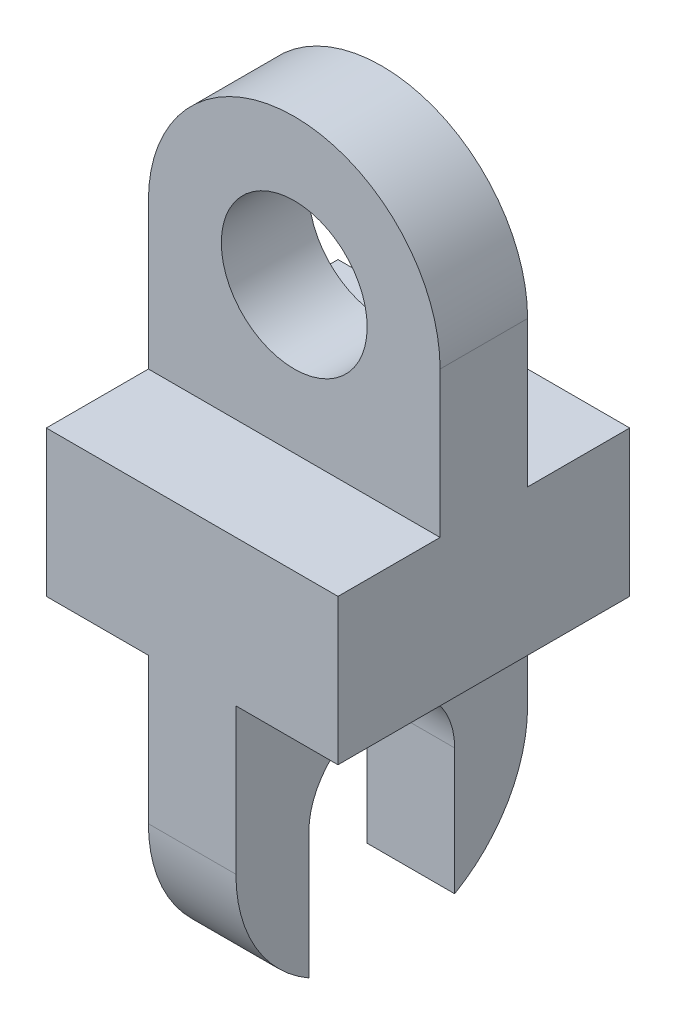
SolidWorks part; units mm, degrees
ref_plane "Alzado" through (0, 0, 0) normal (0, 0, 1) x (1, 0, 0)
ref_plane "Planta" through (0, 0, 0) normal (0, 1, 0) x (1, 0, 0)
ref_plane "Vista lateral" through (0, 0, 0) normal (1, 0, 0) x (0, 0, -1)
sketch "Croquis3" plane through (0, 0, 0) normal (0, 0, 1) x (1, 0, 0)
  line L2 (-50, 100) -> (-50, -100)
  line L3 (-50, -100) -> (50, -100)
  line L4 (50, 100) -> (50, -100)
  arc A0 (50, 100) -> (-50, 100) centre (0, 100) ccw
  point P0 (0, 0)
  dimension "D3" = 100
  dimension "D1" = 100
  dimension "D2" = 200
  dimension "D4" = 50
extrude "Saliente-Extruir1" add sketch "Croquis3" along normal blind 100
sketch "Croquis5" plane through (0, 0, 100) normal (0, 0, 1) x (1, 0, 0)
  line L0 (50, -100) -> (50, 100) construction
  line L2 (-50, 100) -> (-50, 0)
  line L3 (-50, 0) -> (50, 0)
  line L4 (50, 100) -> (50, 0)
  arc A0 (50, 100) -> (-50, 100) centre (0, 100) ccw
  arc A2 (50, 100) -> (-50, 100) centre (0, 100) ccw construction
  point P0 (0, 66.3558)
  dimension "D1" = 100
  dimension "D2" = 100
sketch "Croquis8" plane through (0, 0, 100) normal (0, 0, 1) x (1, 0, 0)
  line L0 (50, 100) -> (50, 0) construction
  line L2 (-50, 100) -> (-50, 50)
  line L3 (-50, 50) -> (50, 50)
  line L4 (50, 100) -> (50, 50)
  arc A0 (50, 100) -> (-50, 100) centre (0, 100) ccw
  arc A1 (50, 100) -> (-50, 100) centre (0, 100) ccw construction
  point P6 (0, 75)
  dimension "D1" = 100
  dimension "D2" = 50
extrude "Cortar-Extruir4" cut sketch "Croquis8" against normal blind 35 and the other way through all
sketch "Croquis9" plane through (0, 0, 0) normal (0, 0, -1) x (-1, 0, 0)
  line L0 (50, 100) -> (50, 0) construction
  line L2 (-50, 100) -> (-50, 50)
  line L3 (-50, 50) -> (50, 50)
  line L4 (50, 100) -> (50, 50)
  arc A0 (50, 100) -> (-50, 100) centre (0, 100) ccw
  arc A1 (50, 100) -> (-50, 100) centre (0, 100) ccw construction
  point P5 (0, 75)
  dimension "D1" = 100
  dimension "D2" = 50
extrude "Cortar-Extruir5" cut sketch "Croquis9" against normal blind 35
sketch "Croquis10" plane through (0, 0, 35) normal (0, 0, -1) x (-1, 0, 0)
  circle A0 centre (0, 100) radius 25
  arc A1 (50, 100) -> (-50, 100) centre (0, 100) ccw construction
  dimension "D1" = 50
extrude "Cortar-Extruir6" cut sketch "Croquis10" against normal through all both and the other way through all
sketch "Croquis12" plane through (-50, 0, 0) normal (-1, 0, 0) x (0, 0, 1)
  line L0 (100, 50) -> (100, -100) construction
  line L1 (0, 0) -> (100, 0)
  line L2 (0, 0) -> (0, -100)
  line L3 (0, -100) -> (100, -100)
  line L4 (100, 0) -> (100, -100)
  line L5 (0, 0) -> (100, -100) construction
  line L6 (0, -100) -> (100, 0) construction
  line L9 (100, -100) -> (0, -100) construction
  point P0 (50, -50)
  dimension "D1" = 100
  dimension "D2" = 0
  dimension "D3" = 100
extrude "Cortar-Extruir10" cut sketch "Croquis12" against normal through all and the other way through all
sketch "Croquis17" plane through (-50, 0, 0) normal (-1, 0, 0) x (0, 0, 1)
  line L0 (0, 50) -> (0, 0) construction
  line L1 (0, 0) -> (100, 0) construction
  line L4 (0, 0) -> (100, 0)
  line L5 (0, 0) -> (0, -50)
  line L7 (100, 0) -> (100, -50)
  arc A0 (0, -50) -> (100, -50) centre (50, -50) ccw
  dimension "D1" = 100
  dimension "D2" = 50
extrude "Saliente-Extruir3" add sketch "Croquis17" against normal blind 100
sketch "Croquis22" plane through (-50, 0, 0) normal (-1, 0, 0) x (0, 0, 1)
  line L0 (0, 50) -> (0, -50) construction
  line L1 (0, 0) -> (100, 0)
  line L2 (0, 0) -> (0, -100)
  line L3 (0, -100) -> (100, -100)
  line L4 (100, 0) -> (100, -100)
  arc A0 (0, -50) -> (100, -50) centre (50, -50) ccw construction
  dimension "D1" = 100
  dimension "D2" = 100
extrude "Cortar-Extruir12" cut sketch "Croquis22" against normal blind 35
sketch "Croquis23" plane through (50, 0, 0) normal (1, 0, 0) x (0, 0, -1)
  line L0 (-100, -50) -> (-100, 50) construction
  line L1 (-100, 0) -> (0, 0)
  line L2 (-100, 0) -> (-100, -100)
  line L3 (-100, -100) -> (0, -100)
  line L4 (0, 0) -> (0, -100)
  arc A0 (-100, -50) -> (0, -50) centre (-50, -50) ccw construction
  dimension "D1" = 100
  dimension "D2" = 100
extrude "Cortar-Extruir13" cut sketch "Croquis23" against normal blind 35
sketch "Croquis24" plane through (-15, 0, 0) normal (-1, 0, 0) x (0, 0, 1)
  line L0 (0, 0) -> (0, -50) construction
  line L1 (65, 150) -> (35, 150) construction
  line L4 (25, -50) -> (25, -110.4288)
  line L5 (25, -110.4288) -> (75, -110.4288)
  line L6 (75, -50) -> (75, -110.4288)
  arc A0 (75, -50) -> (25, -50) centre (50, -50) ccw
  dimension "D1" = 50
  dimension "D2" = 50
  dimension "D3" = 200
  dimension "D4" = 50
  dimension "D5" = 60.4288
extrude "Cortar-Extruir14" cut sketch "Croquis24" against normal through all both and the other way through all
